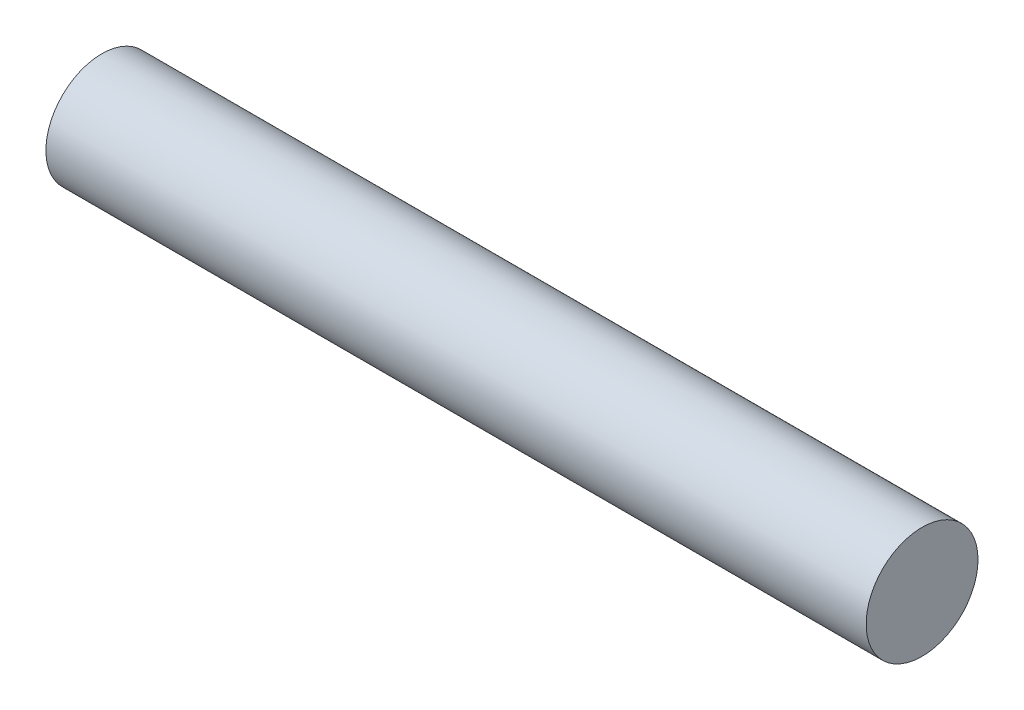
SolidWorks part; units mm, degrees
material "Plain Carbon Steel"
ref_plane "Front Plane" through (0, 0, 0) normal (0, 0, 1) x (1, 0, 0)
ref_plane "Top Plane" through (0, 0, 0) normal (0, 1, 0) x (1, 0, 0)
ref_plane "Right Plane" through (0, 0, 0) normal (1, 0, 0) x (0, 0, -1)
sketch "Sketch1" plane through (0, 0, 0) normal (1, 0, 0) x (0, 0, -1)
  circle A0 centre (0, 0) radius 1.5
  dimension "D1" = 3
extrude "Boss-Extrude1" add sketch "Sketch1" along normal blind 22
